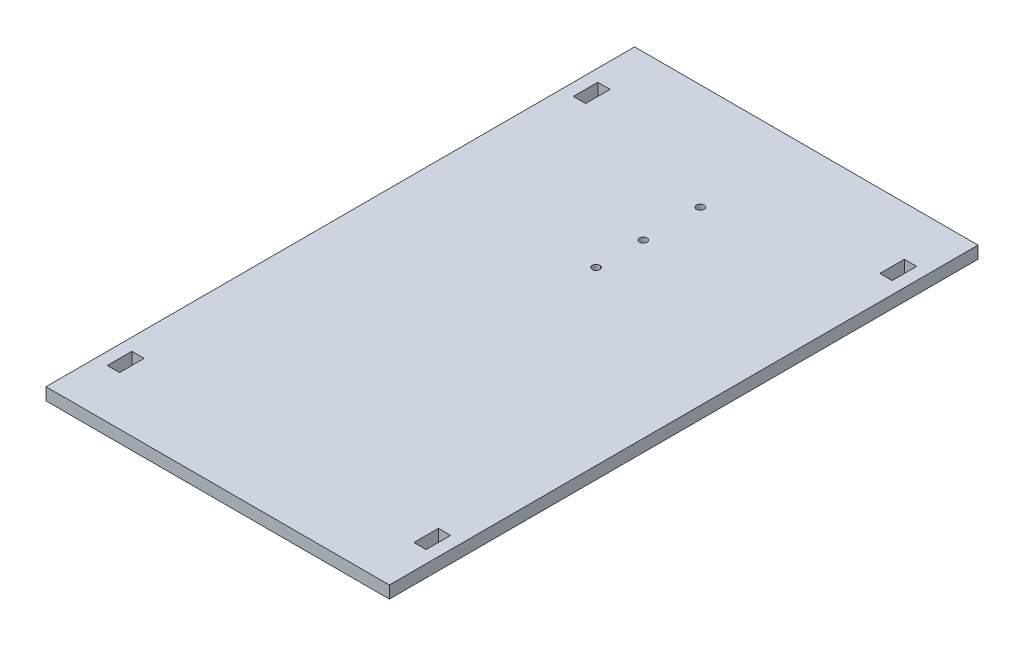
SolidWorks part; units mm, degrees
material "Beech"
ref_plane "Front Plane" through (0, 0, 0) normal (0, 0, 1) x (1, 0, 0)
ref_plane "Top Plane" through (0, 0, 0) normal (0, 1, 0) x (1, 0, 0)
ref_plane "Right Plane" through (0, 0, 0) normal (1, 0, 0) x (0, 0, -1)
sketch "Sketch1" plane through (0, 0, 0) normal (0, 1, 0) x (1, 0, 0)
  line L0 (0, 0) -> (177.8, 0)
  line L1 (0, 0) -> (0, 304.8)
  line L2 (177.8, 0) -> (177.8, 304.8)
  line L3 (0, 304.8) -> (177.8, 304.8)
  line L20 (165.1, 279.4) -> (171.45, 279.4)
  line L21 (165.1, 279.4) -> (165.1, 266.7)
  line L22 (171.45, 279.4) -> (171.45, 266.7)
  line L23 (165.1, 266.7) -> (171.45, 266.7)
  line L24 (6.35, 279.4) -> (12.7, 279.4)
  line L25 (6.35, 279.4) -> (6.35, 266.7)
  line L26 (12.7, 279.4) -> (12.7, 266.7)
  line L27 (6.35, 266.7) -> (12.7, 266.7)
  line L28 (6.35, 38.1) -> (12.7, 38.1)
  line L29 (6.35, 38.1) -> (6.35, 25.4)
  line L30 (12.7, 38.1) -> (12.7, 25.4)
  line L31 (6.35, 25.4) -> (12.7, 25.4)
  line L32 (171.45, 38.1) -> (165.1, 38.1)
  line L33 (171.45, 38.1) -> (171.45, 25.4)
  line L34 (165.1, 38.1) -> (165.1, 25.4)
  line L35 (171.45, 25.4) -> (165.1, 25.4)
  circle A1 centre (88.9, 249.9) radius 1.935
  circle A2 centre (88.9, 220.4) radius 1.935
  circle A3 centre (88.9, 195.9) radius 1.935
  point P21 (88.9, 304.8)
  dimension "D6" = 3.87
  dimension "D2" = 25.4
  dimension "D3" = 29.5
  dimension "D4" = 54.9
  dimension "D5" = 24.5
  dimension "D7" = 304.8
  dimension "D9" = 25.4
  dimension "D12" = 12.7
extrude "Boss-Extrude1" add sketch "Sketch1" along normal blind 6.35
equation "\"CageLeftBottomEdge\"=22.11mm"
equation "\"CageLeftTopEdge\"=22.11mm"
equation "\"CageRightBottomEdge\"=21.63mm"
equation "\"CageRightTopEdge\"=21.63mm"
equation "\"CageHeight\"=86.04mm"
equation "\"CageLength\"=73.76mm"
equation "\"CageTopScrewClearance\"=10mm"
equation "\"CageBottomScrewClearance\"=25mm"
equation "\"CageLeftTopDepth\"= 11.65mm"
equation "\"CageLeftBottomDepth\"=11.11mm"
equation "\"CageLeftTopHeight\"=8.56175mm"
equation "\"CageLeftBottomHeight\"=16mm"
equation "\"CageRightTopDepth\"= 11.05mm"
equation "\"CageRightBottomDepth\"=10.58mm"
equation "\"CageRightTopHeight\"=9.6mm"
equation "\"CageRightBottomHeight\"=15.49mm"
equation "\"CageLeftTopChannelDepth\"=2.41908mm"
equation "\"CageLeftBottomChannelDepth\"=2.588mm"
equation "\"CageLeftChannelHeight\"=11.7mm"
equation "\"CageRightTopChannelDepth\"=2.32mm"
equation "\"CageRightBottomChannelDepth\"=2.318mm"
equation "\"CageRightChannelHeight\"=10mm"
equation "\"CageChanRelHeight\"=23.99mm"
equation "\"CageChanRelDepth\"=5.492mm"
equation "\"CageChamberRadius\"=16.261mm"
equation "\"CageScrewDiameter\"=4.8mm"
equation "\"CageSetScrewDiameter\"=3.5mm"
equation "\"CageAxleRadius\"=6.639mm"
equation "\"CageAxleKeyHeight\"=1.619mm"
equation "\"CageAxleKeyWidth\"=2.662mm"
equation "\"CageHoseWindowWidth\"=16.29mm"
equation "\"CageHoseWindowHeight\"=26.5mm"
equation "\"CageHoseWindow-Edge\"=8.89mm"
equation "\"CageScrew-VerticalEdge\"=5.0mm"
equation "\"CageScrew-HorizontalEdge\"=7.5mm"
equation "\"CageScrew-HoseCornerScrewEdge\"=4.45mm"
equation "\"CageAxle-BottomEdge\"=56.05mm"
equation "\"CageAxle-FrontEdge\"=46.03mm"
equation "\"CageBackSetScrew-Axle\"=40mm"
equation "\"CageFrontSetScrew-Axle\"=22mm"
equation "\"CageVelocityWindow-BackEdge\"=34.8mm"
equation "\"CageVelocityWindow-BottomEdge\"=27.55mm"
equation "\"CageVelocityWindowHeight\"=22.29mm"
equation "\"CageVelocityWindowWidth\"=12.61mm"
equation "\"TriggerSlot-BottomEdge\"=6.35mm"
equation "\"TriggerSlot-FrontEdge\"=15mm"
equation "\"TriggerSlotSize\"=6.7mm"
equation "\"TriggerRackOffset\"=.236224in"
equation "\"TriggerSlotSizeInt\"=.25in"
equation "\"MotorMountLegLength\"=.25in"
equation "\"GearOffset\"=.264907in"
equation "\"TriggerSlotSpacing\"=.25in"
equation "\"TriggerMiniSlotWidth\"=3.5mm"
equation "\"TriggerRackWidth\"=6.5mm"
equation "\"TGMGearFaceDiameter\"=24.40mm"
equation "\"TGMCylinderLength\"=15.00mm"
equation "\"TGMScrewHole-Center\"=8.70mm"
equation "\"TGMScrewHoleDiameter\"=5.04mm"
equation "\"TGMCenterHoleDiameter\"=9.50mm"
equation "\"TGMShaftCollarSideLength\"=19.00mm"
equation "\"TGMShaftCollarDockingDepth\"=7.00mm"
equation "\"whitemotordepth\"=11.27mm"
equation "\"whitemotorbackdepth\"=3.845mm"
equation "\"whitemotoraxledepth\" = 3.5mm"
equation "\"whitemotoraxleoffset\"=11.4mm"
equation "\"whitemotorwidth\"=12.07mm"
equation "\"whitemotorheight\"=16.68mm"
equation "\"whitemotorcylinderlength\" =13.04mm"
equation "\"whitemotorcylinderradius\"=3.845mm"
equation "\"whitemotorcylinderoffset\"=2.35mm"
equation "\"whitemotorcutoutlength\"=1.88mm"
equation "\"whitemotorouterrad\"=5mm"
equation "\"whitemotorinnerrad\"=2.95mm"
equation "\"elasticracklength\"=2in"
equation "\"elasticrackpegsize\"=.25in"
equation "\"elasticrackpegbuffer\"=.125in"
equation "\"elasticrackpegspacing\"=1.76476378in"
equation "\"elasticbaybuffer\"=.25in"
equation "\"elasticdepth\"=.125in"
equation "\"elasticbaydepth\"=.75in"
equation "\"motormountwidth\"=12mm"
equation "\"motormountcornerfillet\"=3mm"
equation "\"pandiscradius\"=14in"
equation "\"towermaterialwidth\"=.25in"
equation "\"towerslotlength\"=.5in"
equation "\"towermarkerspace\"=5in"
equation "\"towerslothorizoffset\"=1in"
equation "\"towerslothorizspacing\"=2in"
equation "\"towerslotvertoffset\"=3in"
equation "\"towerslotvertspacing\"=1in"
equation "\"towerheight\"=12in"
equation "\"towerupslot\"=1in"
equation "\"D2@Sketch1\"=\"towerupslot\""
equation "\"D3@Sketch1\"=\"ajax4020gap\""
equation "\"D4@Sketch1\"=\"ajax4020gap\"+1in"
equation "\"D5@Sketch1\"=\"ajax4010gap\""
equation "\"D6@Sketch1\"=\"ajaxaxlesize\""
equation "\"D7@Sketch1\"=\"towerheight\""
equation "\"toweraxle\"=.5in"
equation "\"D9@Sketch1\"=\"towerupslot\""
equation "\"towerplatslotoffset\"=1.5in"
equation "\"D12@Sketch1\"=\"towerslotlength\""
equation "\"D1@Boss-Extrude1\"=\"towermaterialwidth\""
equation "\"towermotorpanelheight\"=10in"
equation "\"towerplatdepth\"=2in"
equation "\"stepperouterrad\"=10mm"
equation "\"stepperscrewsize\"=3.45mm"
equation "\"stepperscrewc2c\"=49.5mm"
equation "\"stepperdepthoffset\"=24mm"
equation "\"stepperhorizoffset\"=22.91mm"
equation "\"shaftslotOD\"=18.8mm"
equation "\"shaftslotID\"=13.28mm"
equation "\"shaftkeywidth\"=2.67mm"
equation "\"shaftkeydepth\"=1.8mm"
equation "\"shaftcollartotaldepth\"=12.5mm"
equation "\"shaftsquaredepth\"=6mm"
equation "\"shaftsetscrewsize\"=3.5mm"
equation "\"shaftkeytightdepth\"=1.85mm"
equation "\"shaftslottightID\"=12.78mm"
equation "\"shaftsetscrewoffset\"=9mm"
equation "\"cagecollartotaldepth\"=10mm"
equation "\"cagecollartotalwidth\"=35mm"
equation "\"cagecollarbasedepth\"=4mm"
equation "\"ajaxaxlesize\"=3.87mm"
equation "\"ajax4020gap\"=29.5mm"
equation "\"ajax4010gap\"=24.5mm"
equation "\"ajaxinnercut\"=2.3mm"
equation "\"ajaxwidth\"=6.1mm"
equation "\"ajaxdiametral\"=25.8854"
equation "\"ajaxhubdepth\"=.25in"
equation "\"ajaxcutoutdepth\"=2.3mm"
equation "\"ajax20hubbuffer\"=0.240157in"
equation "\"ajax20hubholeoffset\"=.19685in"
equation "\"ajax20hubholesize\"=.059055in"
equation "\"ajax20cutoutint\"=13.4mm"
equation "\"ajax40hubholesize\"=7.21mm"
equation "\"ajax40hubholeoffset\"=10mm"
equation "\"ajax40hubbuffer\"=.350394in"
equation "\"ajax40cutoutint\"=32.6mm"
equation "\"no6diam\"=.146in"
equation "\"shconangle\"=20deg"
equation "\"shconlen\"=1in"
equation "\"lnconlen\"=1.5in"
equation "\"lnconangle\"=15deg"
